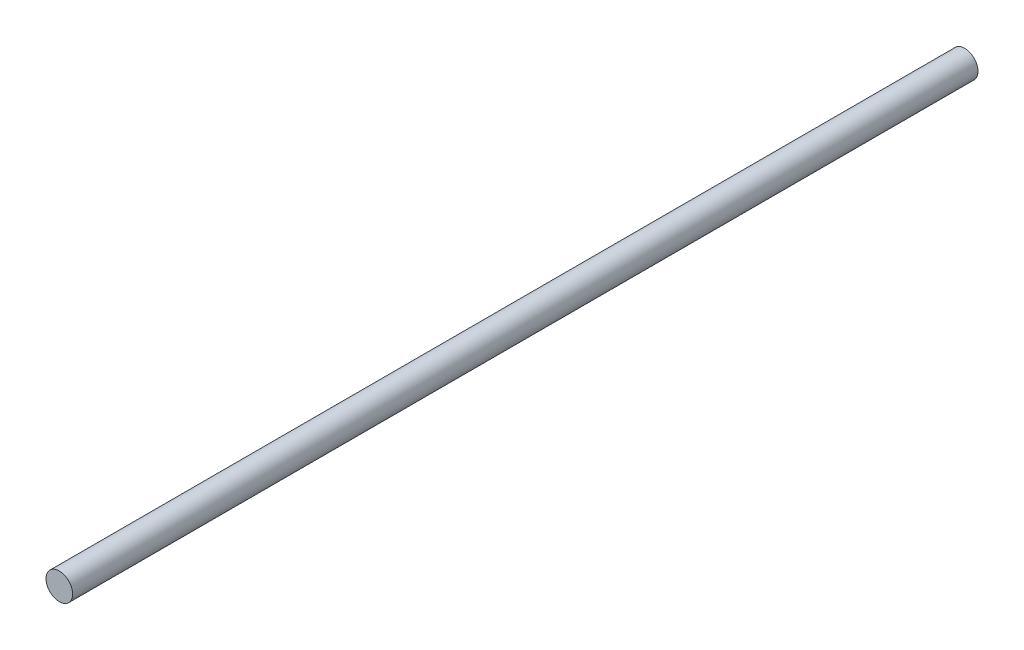
SolidWorks part; units mm, degrees
material "Cast Alloy Steel"
ref_plane "Front Plane" through (0, 0, 0) normal (0, 0, 1) x (1, 0, 0)
ref_plane "Top Plane" through (0, 0, 0) normal (0, 1, 0) x (1, 0, 0)
ref_plane "Right Plane" through (0, 0, 0) normal (1, 0, 0) x (0, 0, -1)
sketch "Sketch1" plane through (0, 0, 0) normal (0, 0, 1) x (1, 0, 0)
  circle A0 centre (-582.3699, 124.9106) radius 4
extrude "Boss-Extrude1" add sketch "Sketch1" along normal up to surface (272 mm away)
